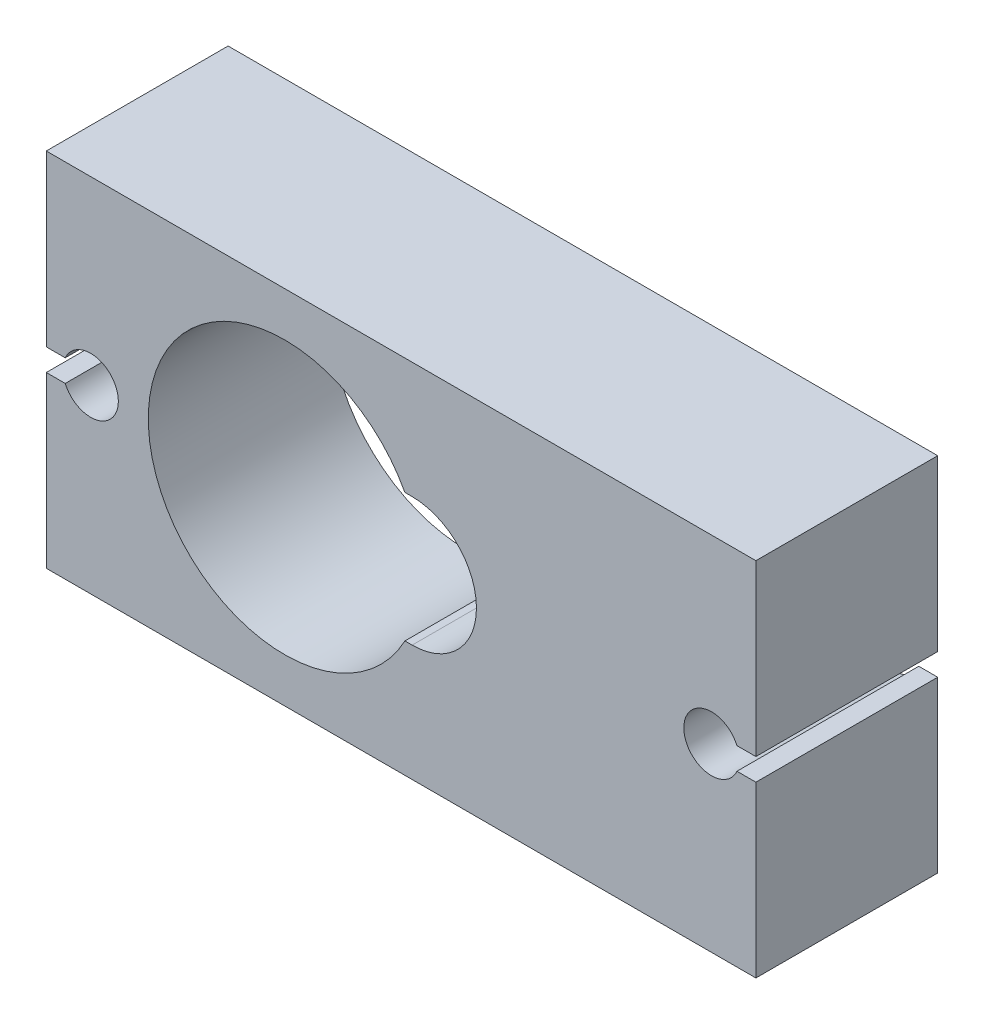
SolidWorks part; units mm, degrees
ref_plane "Front Plane" through (0, 0, 0) normal (0, 0, 1) x (1, 0, 0)
ref_plane "Top Plane" through (0, 0, 0) normal (0, 1, 0) x (1, 0, 0)
ref_plane "Right Plane" through (0, 0, 0) normal (1, 0, 0) x (0, 0, -1)
sketch "Sketch1" plane through (0, 0, 0) normal (0, 0, 1) x (1, 0, 0)
  line L0 (3.0028, 5.748) -> (-25, 5.748) construction
  line L1 (5.0028, -2.4) -> (-27, -2.4)
  line L2 (-10.5, 8.65) -> (-11.0719, 8.65) construction
  line L3 (-11.0719, 2.85) -> (-10.5, 2.85) construction
  line L4 (-27, 13.9) -> (5.0028, 13.9)
  line L5 (-0.3251, 11.9) -> (-26.172, 11.9) construction
  line L6 (-2.7838, -0.4) -> (-28.6877, -0.4) construction
  line L7 (5.0028, 13.9) -> (5.0028, 6.248)
  line L8 (5.0028, 5.248) -> (5.0028, -2.4)
  line L9 (-27, 13.9) -> (-27, 6.248)
  line L10 (-27, 5.248) -> (-27, -2.4)
  line L23 (-26.1456, 5.248) -> (-27, 5.248)
  line L29 (-27, 6.248) -> (-26.1456, 6.248)
  line L32 (-10.5, 8.25) -> (-11.0719, 8.25) construction
  line L33 (-11.0719, 3.25) -> (-10.5, 3.25) construction
  line L37 (-11.0719, 8.25) -> (-10.5, 8.25) construction
  line L38 (-10.5, 3.25) -> (-11.0719, 3.25) construction
  line L39 (4.1485, 6.248) -> (5.0028, 6.248)
  line L45 (5.0028, 5.248) -> (4.1485, 5.248)
  line L47 (-10.5, 8.65) -> (-10.8267, 8.65)
  line L48 (-10.8267, 2.85) -> (-10.5, 2.85)
  arc A0 (-10.7117, 8.4239) -> (-10.7117, 3.0761) centre (-16.25, 5.75) ccw construction
  arc A8 (-26.1456, 5.248) -> (-26.1456, 6.248) centre (-25, 5.748) ccw
  arc A9 (-16.25, 11.5) -> (-22, 5.75) centre (-16.25, 5.75) ccw construction
  arc A10 (-10.5, 3.25) -> (-10.5, 8.25) centre (-10.5, 5.75) ccw construction
  arc A11 (-11.0719, 8.25) -> (-11.0719, 3.25) centre (-16.25, 5.75) ccw construction
  arc A12 (-16.25, 0) -> (-11.0719, 3.25) centre (-16.25, 5.75) ccw construction
  arc A13 (-11.0719, 8.25) -> (-16.25, 11.5) centre (-16.25, 5.75) ccw construction
  arc A14 (-10.5, 3.25) -> (-10.5, 8.25) centre (-10.5, 5.75) ccw construction
  arc A15 (4.1485, 6.248) -> (4.1485, 5.248) centre (3.0028, 5.748) ccw
  arc A16 (-10.8267, 8.65) -> (-10.8267, 2.85) centre (-16.25, 5.75) ccw
  arc A17 (-10.5, 2.85) -> (-10.5, 8.65) centre (-10.5, 5.75) ccw
  dimension "D4" = 32.0028
  dimension "D2" = 2
  dimension "D3" = 2
  dimension "D1" = 0.4
extrude "Boss-Extrude1" add sketch "Sketch1" along normal blind 8.2
